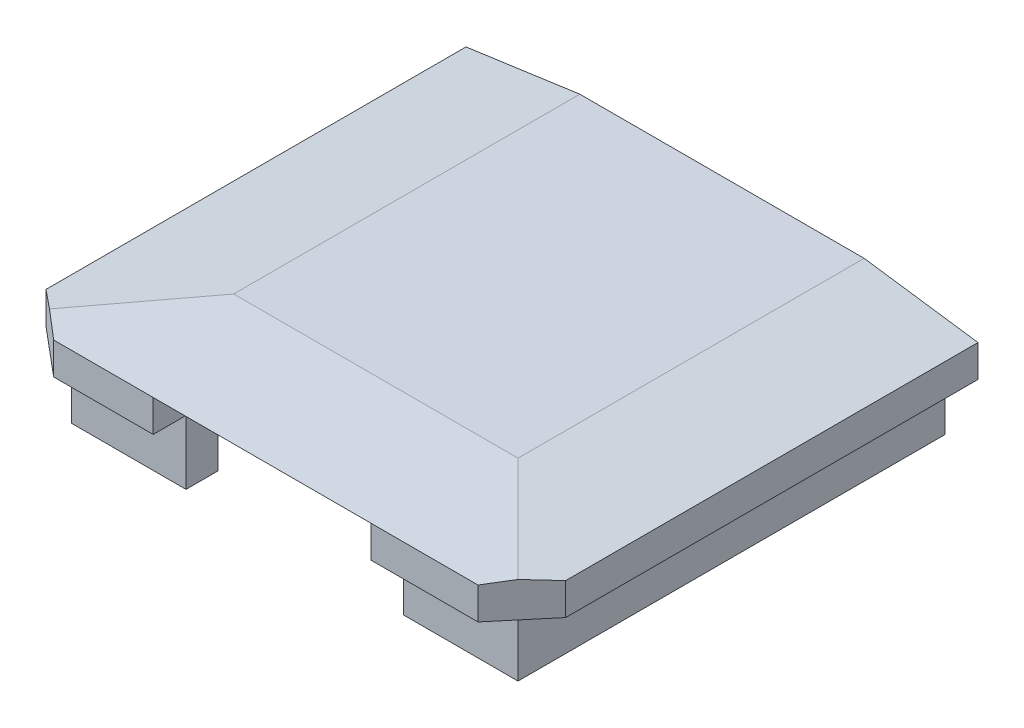
SolidWorks part; units mm, degrees
ref_plane "Front Plane" through (0, 0, 0) normal (0, 0, 1) x (1, 0, 0)
ref_plane "Top Plane" through (0, 0, 0) normal (0, 1, 0) x (1, 0, 0)
ref_plane "Right Plane" through (0, 0, 0) normal (1, 0, 0) x (0, 0, -1)
sketch "Sketch1" plane through (0, 0, 0) normal (0, 1, 0) x (1, 0, 0)
  line L1 (-16, 24) -> (16, 24)
  line L2 (-16, 24) -> (-16, -24)
  line L3 (-16, -24) -> (16, -24)
  line L4 (16, 24) -> (16, -24)
  line L5 (-16, 24) -> (16, -24) construction
  line L6 (-16, -24) -> (16, 24) construction
  point P1 (0, 0)
  dimension "D1" = 32
  dimension "D2" = 48
extrude "Boss-Extrude1" add sketch "Sketch1" along normal blind 3
sketch "Sketch2" plane through (0, 0, 0) normal (0, -1, 0) x (1, 0, 0)
  line L0 (-13.95, -21.95) -> (-11.95, -21.95)
  line L1 (-11.95, -21.95) -> (-11.95, -19.95)
  line L2 (11.95, -19.95) -> (11.95, -21.95)
  line L3 (11.95, -21.95) -> (13.95, -21.95)
  line L4 (11.95, -19.95) -> (11.95, 19.95)
  line L5 (11.95, 19.95) -> (6.8, 19.95)
  line L6 (-11.95, 19.95) -> (-11.95, -19.95)
  line L8 (13.95, -21.95) -> (13.95, 21.95)
  line L9 (13.95, 21.95) -> (-13.95, 21.95)
  line L10 (-13.95, 21.95) -> (-13.95, -21.95)
  line L11 (-13.95, -21.95) -> (13.95, -21.95)
  line L12 (13.95, -21.95) -> (13.95, 21.95)
  line L13 (13.95, 21.95) -> (6.8, 21.95)
  line L14 (-13.95, 21.95) -> (-13.95, -21.95)
  line L16 (-6.8, 21.95) -> (-6.8, 19.95)
  line L17 (6.8, 21.95) -> (6.8, 19.95)
  line L18 (0, 0) -> (0, 24) construction
  line L19 (-16, 24) -> (16, 24) construction
  line L20 (-6.8, 21.95) -> (-13.95, 21.95)
  line L21 (13.95, 21.95) -> (-13.95, 21.95) construction
  line L22 (-6.8, 19.95) -> (-11.95, 19.95)
  line L23 (11.95, 19.95) -> (-11.95, 19.95) construction
  line L27 (-11.95, -19.95) -> (11.95, -19.95) construction
  line L28 (-13.95, -21.95) -> (13.95, -21.95) construction
  point P17 (-6.8, 20.95)
  dimension "D3" = 13.6
  dimension "D1" = 2.05
  dimension "D2" = 2
extrude "Boss-Extrude2" add sketch "Sketch2" along normal blind 4
chamfer "Chamfer1" distance 1 angle 82 2 edges at (0, 3, 24) (0, 3, -24)
chamfer "Chamfer2" distance 1 angle 82 2 edges at (16, 3, 0) (-16, 3, 0)
sketch "Sketch4" plane through (0, 0, 24) normal (0, 0, 1) x (1, 0, 0)
  line L6 (0, 0) -> (0, -3.2251) construction
  line L7 (-6.8, 0) -> (6.8, 0)
  line L8 (6.8, 0) -> (6.8, 2)
  line L9 (6.8, 2) -> (-6.8, 2)
  line L10 (-6.8, 2) -> (-6.8, 0)
  point P6 (0, 0)
  dimension "D1" = 2
extrude "Cut-Extrude2" cut sketch "Sketch4" against normal blind 7
chamfer "Chamfer4" distance 2.5 angle 50 2 edges at (16, 1, 24) (-16, 1, 24)
chamfer "Chamfer5" distance 2.5 angle 45 2 edges at (-16, 1, -24) (16, 1, -24)
sketch "Sketch5" plane through (0, 3, 0) normal (0, 1, 0) x (1, 0, 0)
  line L0 (-21.6753, 4.7479) -> (23.6708, 4.7479)
  line L1 (23.6708, 4.7479) -> (23.6708, 26.4921)
  line L2 (23.6708, 26.4921) -> (-21.6753, 26.4921)
  line L3 (-21.6753, 26.4921) -> (-21.6753, 4.7479)
  point P2 (0, 0)
  point P6 (-21.6753, 5.2296)
extrude "Cut-Extrude3" cut sketch "Sketch5" against normal blind 10
